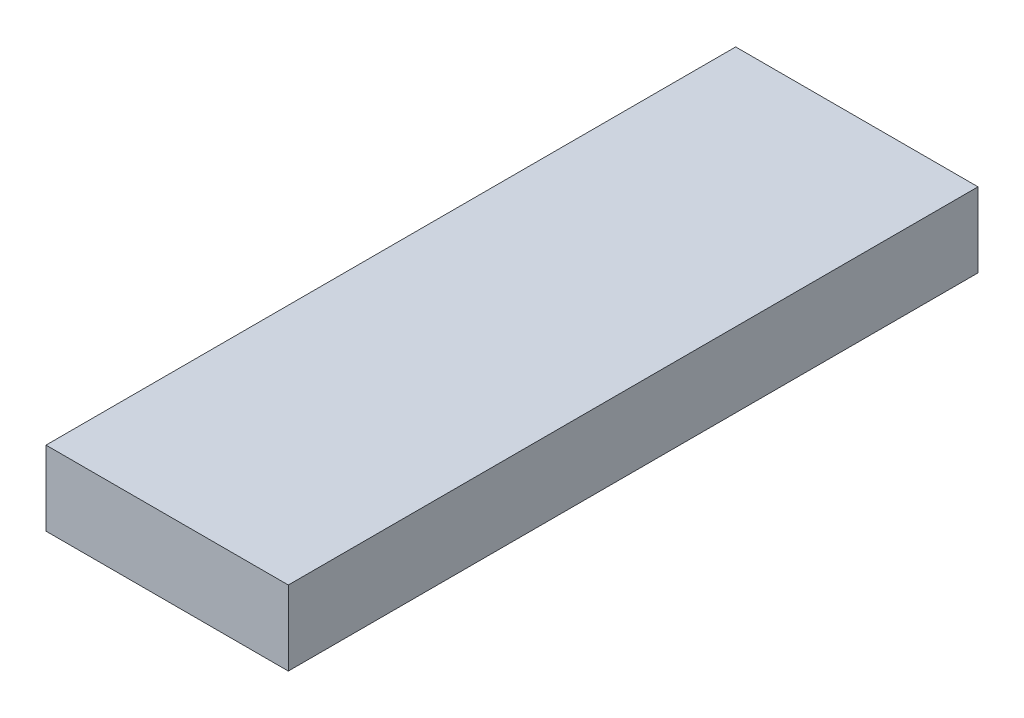
SolidWorks part; units mm, degrees
material "A-Glass Fiber"
ref_plane "Front Plane" through (0, 0, 0) normal (0, 0, 1) x (1, 0, 0)
ref_plane "Top Plane" through (0, 0, 0) normal (0, 1, 0) x (1, 0, 0)
ref_plane "Right Plane" through (0, 0, 0) normal (1, 0, 0) x (0, 0, -1)
sketch "Sketch1" plane through (0, 0, 0) normal (0, 1, 0) x (1, 0, 0)
  line L1 (0, 0) -> (330.2, 0)
  line L2 (0, 0) -> (0, 939.8)
  line L3 (0, 939.8) -> (330.2, 939.8)
  line L4 (330.2, 0) -> (330.2, 939.8)
  dimension "D1" = 330.2
  dimension "D2" = 939.8
extrude "Boss-Extrude1" add sketch "Sketch1" along normal blind 101.6
